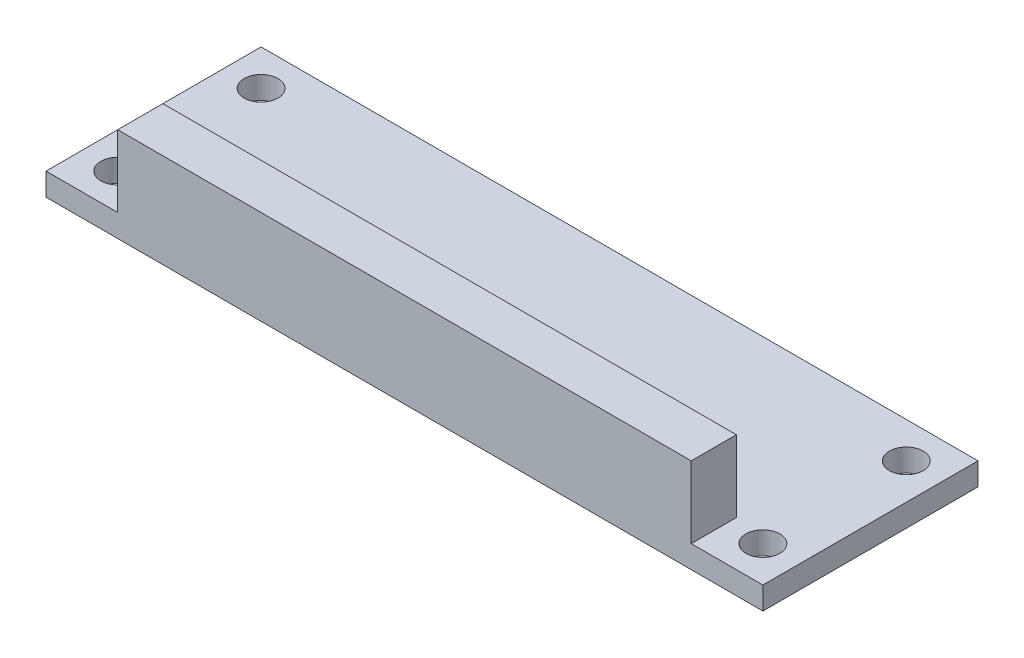
SolidWorks part; units mm, degrees
material "ABS"
ref_plane "Front Plane" through (0, 0, 0) normal (0, 0, 1) x (1, 0, 0)
ref_plane "Top Plane" through (0, 0, 0) normal (0, 1, 0) x (1, 0, 0)
ref_plane "Right Plane" through (0, 0, 0) normal (1, 0, 0) x (0, 0, -1)
sketch "Sketch4" plane through (0, 0, 0) normal (0, 1, 0) x (1, 0, 0)
  line L0 (28.575, 6.35) -> (28.575, -6.35) construction
  line L1 (-31.75, -9.525) -> (31.75, -9.525)
  line L2 (-31.75, -9.525) -> (-31.75, 9.525)
  line L3 (-31.75, 9.525) -> (31.75, 9.525)
  line L4 (31.75, -9.525) -> (31.75, 9.525)
  line L5 (-31.75, -9.525) -> (31.75, 9.525) construction
  line L6 (-31.75, 9.525) -> (31.75, -9.525) construction
  line L7 (0, 0) -> (28.575, 0) construction
  line L8 (0, 9.525) -> (0, -9.525) construction
  line L9 (-28.575, 6.35) -> (-28.575, -6.35) construction
  circle A0 centre (28.575, 6.35) radius 1.5
  circle A1 centre (28.575, -6.35) radius 1.5
  circle A2 centre (-28.575, -6.35) radius 1.5
  circle A3 centre (-28.575, 6.35) radius 1.5
  point P0 (0, 0)
  dimension "D4" = 3
  dimension "D1" = 63.5
  dimension "D2" = 19.05
  dimension "D3" = 12.7
  dimension "D5" = 3.175
extrude "Boss-Extrude2" add sketch "Sketch4" along normal blind 2
sketch "Sketch6" plane through (0, 2, 0) normal (0, 1, 0) x (1, 0, 0)
  line L0 (-31.75, -9.525) -> (31.75, -9.525) construction
  line L1 (-25.4, -9.525) -> (25.4, -9.525)
  line L2 (-25.4, -9.525) -> (-25.4, -5.525)
  line L3 (-25.4, -5.525) -> (25.4, -5.525)
  line L4 (25.4, -9.525) -> (25.4, -5.525)
  line L5 (0, -5.525) -> (0, 9.525) construction
  line L6 (31.75, 9.525) -> (-31.75, 9.525) construction
  dimension "D1" = 4
  dimension "D2" = 50.8
extrude "Boss-Extrude3" add sketch "Sketch6" along normal blind 6.35
equation "\"D5@Sketch4\"=0.125"
